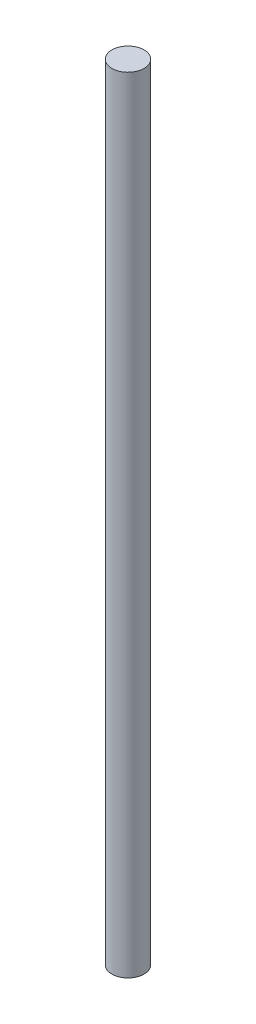
SolidWorks part; units mm, degrees
ref_plane "Front Plane" through (0, 0, 0) normal (0, 0, 1) x (1, 0, 0)
ref_plane "Top Plane" through (0, 0, 0) normal (0, 1, 0) x (1, 0, 0)
ref_plane "Right Plane" through (0, 0, 0) normal (1, 0, 0) x (0, 0, -1)
sketch "Sketch1" plane through (0, 0, 0) normal (0, 1, 0) x (1, 0, 0)
  circle A0 centre (0, 0) radius 4
  dimension "D1" = 8
extrude "Boss-Extrude1" add sketch "Sketch1" along normal blind 195
